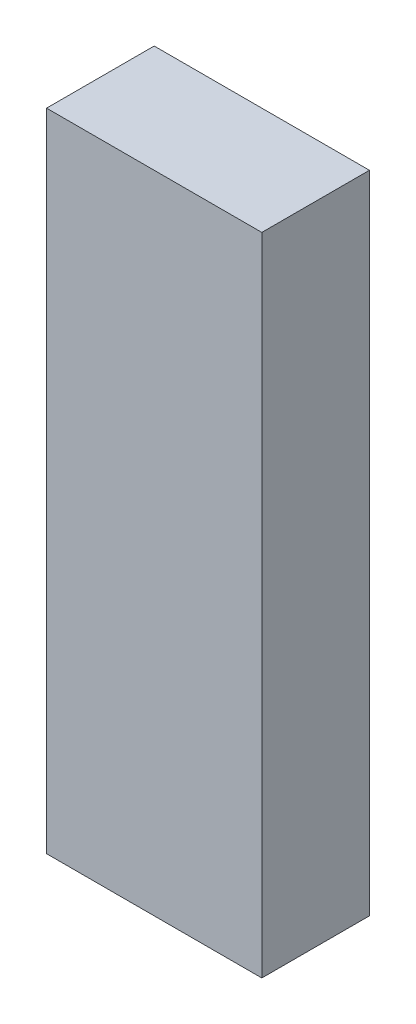
SolidWorks part; units mm, degrees
ref_plane "Plan de face" through (0, 0, 0) normal (0, 0, 1) x (1, 0, 0)
ref_plane "Plan de dessus" through (0, 0, 0) normal (0, 1, 0) x (1, 0, 0)
ref_plane "Plan de droite" through (0, 0, 0) normal (1, 0, 0) x (0, 0, -1)
sketch "Esquisse1" plane through (0, 0, 0) normal (0, 0, 1) x (1, 0, 0)
  line L1 (-64.0974, 4.4076) -> (-54.0974, 4.4076)
  line L2 (-64.0974, 4.4076) -> (-64.0974, -25.5924)
  line L3 (-64.0974, -25.5924) -> (-54.0974, -25.5924)
  line L4 (-54.0974, 4.4076) -> (-54.0974, -25.5924)
extrude "Boss.-Extru.1" add sketch "Esquisse1" along normal blind 5
